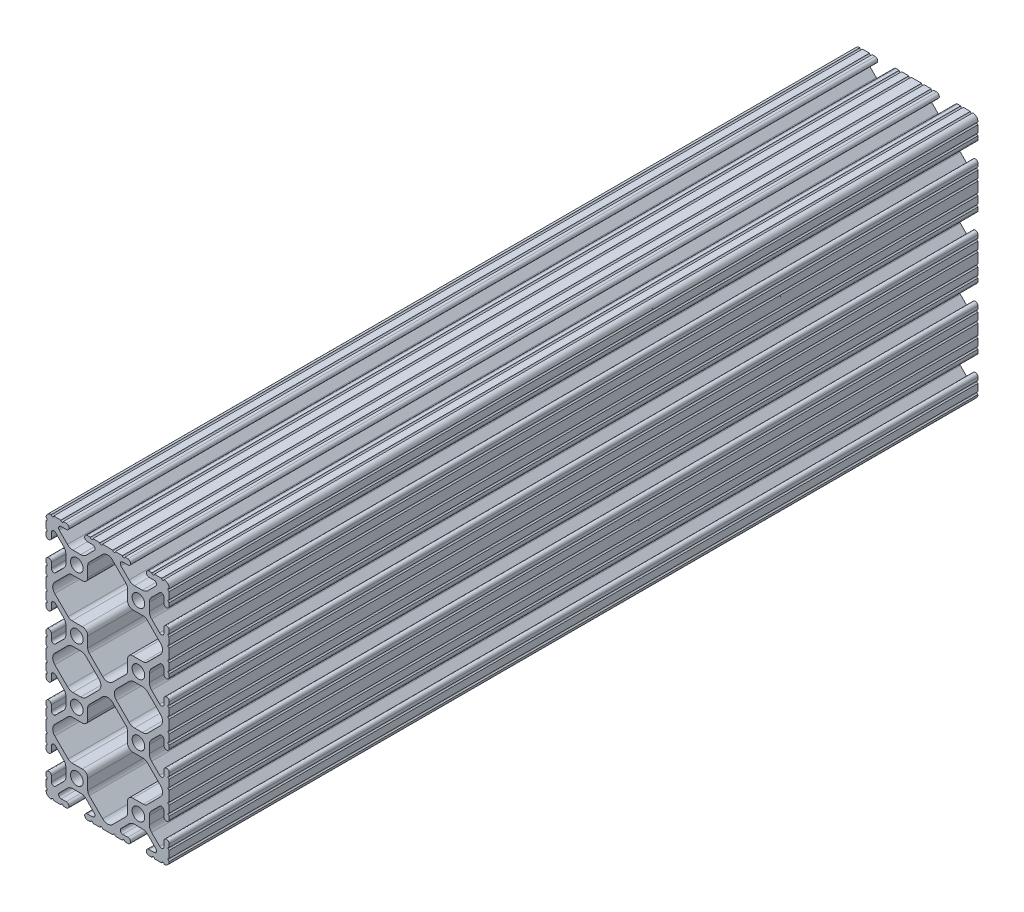
SolidWorks part; units mm, degrees
ref_plane "Front Plane" through (0, 0, 0) normal (0, 0, 1) x (1, 0, 0)
ref_plane "Top Plane" through (0, 0, 0) normal (0, 1, 0) x (1, 0, 0)
ref_plane "Right Plane" through (0, 0, 0) normal (1, 0, 0) x (0, 0, -1)
sketch "Sketch1" plane through (0, 0, 0) normal (0, 0, 1) x (1, 0, 0)
  line L0 (2.286, 55.2958) -> (-2.0184, 55.2958)
  line L1 (-3.5809, 55.943) -> (-9.0725, 61.4345)
  line L2 (-9.0725, 65.5655) -> (-3.5809, 71.057)
  line L3 (-2.0184, 71.7042) -> (2.286, 71.7042)
  line L4 (4.4958, 73.914) -> (4.4958, 78.2184)
  line L5 (5.143, 79.7809) -> (10.6345, 85.2725)
  line L6 (14.7655, 85.2725) -> (20.257, 79.7809)
  line L7 (20.9042, 78.2184) -> (20.9042, 73.914)
  line L8 (23.114, 71.7042) -> (27.4184, 71.7042)
  line L9 (28.9809, 71.057) -> (34.4725, 65.5655)
  line L10 (34.4725, 61.4345) -> (28.9809, 55.943)
  line L11 (27.4184, 55.2958) -> (23.114, 55.2958)
  line L12 (20.9042, 53.086) -> (20.9042, 48.7816)
  line L13 (20.257, 47.2191) -> (14.7655, 41.7275)
  line L14 (10.6345, 41.7275) -> (5.143, 47.2191)
  line L15 (4.4958, 48.7816) -> (4.4958, 53.086)
  line L16 (4.4958, 23.114) -> (4.4958, 27.4184)
  line L17 (5.143, 28.9809) -> (10.6345, 34.4725)
  line L18 (14.7655, 34.4725) -> (20.257, 28.9809)
  line L19 (20.9042, 27.4184) -> (20.9042, 23.114)
  line L20 (23.114, 20.9042) -> (27.4184, 20.9042)
  line L21 (28.9809, 20.257) -> (34.4725, 14.7655)
  line L22 (34.4725, 10.6345) -> (28.9809, 5.143)
  line L23 (27.4184, 4.4958) -> (23.114, 4.4958)
  line L24 (20.9042, 2.286) -> (20.9042, -2.0184)
  line L25 (20.257, -3.5809) -> (14.7655, -9.0725)
  line L26 (10.6345, -9.0725) -> (5.143, -3.5809)
  line L27 (4.4958, -2.0184) -> (4.4958, 2.286)
  line L28 (2.286, 4.4958) -> (-2.0184, 4.4958)
  line L29 (-3.5809, 5.143) -> (-9.0725, 10.6345)
  line L30 (-9.0725, 14.7655) -> (-3.5809, 20.257)
  line L31 (-2.0184, 20.9042) -> (2.286, 20.9042)
  line L32 (27.0186, 29.8958) -> (23.7824, 29.8958)
  line L33 (21.5373, 30.8258) -> (16.3286, 36.0346)
  line L34 (16.3286, 40.1654) -> (21.5373, 45.3742)
  line L35 (23.7824, 46.3042) -> (27.0186, 46.3042)
  line L36 (29.2636, 45.3743) -> (34.4725, 40.1655)
  line L37 (34.4725, 36.0345) -> (29.2636, 30.8257)
  line L38 (1.6176, 29.8958) -> (-1.6186, 29.8958)
  line L39 (-3.8636, 30.8257) -> (-9.0725, 36.0345)
  line L40 (-9.0725, 40.1655) -> (-3.8636, 45.3743)
  line L41 (-1.6186, 46.3042) -> (1.6176, 46.3042)
  line L42 (3.8627, 45.3742) -> (9.0714, 40.1654)
  line L43 (9.0714, 36.0346) -> (3.8627, 30.8258)
  line L44 (-12.7, 40.2336) -> (-12.7, 35.9664)
  line L45 (-12.7, 34.9504) -> (-12.7, 32.004)
  line L46 (-12.7, 30.988) -> (-12.7, 29.7434)
  line L47 (-10.4902, 29.7434) -> (-10.4902, 31.8743)
  line L48 (-8.7558, 32.5927) -> (-5.4258, 29.2627)
  line L49 (-4.4958, 27.0176) -> (-4.4958, 23.7824)
  line L50 (-5.4258, 21.5373) -> (-8.7558, 18.2073)
  line L51 (-10.4902, 18.9257) -> (-10.4902, 21.0566)
  line L52 (-12.7, 21.0566) -> (-12.7, 19.812)
  line L53 (-12.7, 18.796) -> (-12.7, 15.8496)
  line L54 (-12.7, 14.8336) -> (-12.7, 10.5664)
  line L55 (-12.7, 9.5504) -> (-12.7, 6.604)
  line L56 (-12.7, 5.588) -> (-12.7, 4.3434)
  line L57 (-10.4902, 4.3434) -> (-10.4902, 6.4743)
  line L58 (-8.7558, 7.1927) -> (-5.4258, 3.8627)
  line L59 (-4.4958, 1.6176) -> (-4.4958, -1.6176)
  line L60 (-5.4258, -3.8627) -> (-8.7558, -7.1927)
  line L61 (-10.4902, -6.4743) -> (-10.4902, -4.3434)
  line L62 (-12.7, -4.3434) -> (-12.7, -5.588)
  line L63 (-12.7, -6.604) -> (-12.7, -9.5504)
  line L64 (-9.5504, -12.7) -> (-6.604, -12.7)
  line L65 (-5.588, -12.7) -> (-4.3434, -12.7)
  line L66 (-4.3434, -10.4902) -> (-6.4743, -10.4902)
  line L67 (-7.1927, -8.7558) -> (-3.8627, -5.4258)
  line L68 (-1.6176, -4.4958) -> (1.6176, -4.4958)
  line L69 (3.8627, -5.4258) -> (7.1927, -8.7558)
  line L70 (6.4743, -10.4902) -> (4.3434, -10.4902)
  line L71 (4.3434, -12.7) -> (5.588, -12.7)
  line L72 (6.604, -12.7) -> (9.5504, -12.7)
  line L73 (10.5664, -12.7) -> (14.8336, -12.7)
  line L74 (15.8496, -12.7) -> (18.796, -12.7)
  line L75 (19.812, -12.7) -> (21.0566, -12.7)
  line L76 (21.0566, -10.4902) -> (18.9257, -10.4902)
  line L77 (18.2073, -8.7558) -> (21.5373, -5.4258)
  line L78 (23.7824, -4.4958) -> (27.0176, -4.4958)
  line L79 (29.2627, -5.4258) -> (32.5927, -8.7558)
  line L80 (31.8743, -10.4902) -> (29.7434, -10.4902)
  line L81 (29.7434, -12.7) -> (30.988, -12.7)
  line L82 (32.004, -12.7) -> (34.9504, -12.7)
  line L83 (38.1, -9.5504) -> (38.1, -6.604)
  line L84 (38.1, -5.588) -> (38.1, -4.3434)
  line L85 (35.8902, -4.3434) -> (35.8902, -6.4743)
  line L86 (34.1558, -7.1927) -> (30.8258, -3.8627)
  line L87 (29.8958, -1.6176) -> (29.8958, 1.6176)
  line L88 (30.8258, 3.8627) -> (34.1558, 7.1927)
  line L89 (35.8902, 6.4743) -> (35.8902, 4.3434)
  line L90 (38.1, 4.3434) -> (38.1, 5.588)
  line L91 (38.1, 6.604) -> (38.1, 9.5504)
  line L92 (38.1, 10.5664) -> (38.1, 14.8336)
  line L93 (38.1, 15.8496) -> (38.1, 18.796)
  line L94 (38.1, 19.812) -> (38.1, 21.0566)
  line L95 (35.8902, 21.0566) -> (35.8902, 18.9257)
  line L96 (34.1558, 18.2073) -> (30.8258, 21.5373)
  line L97 (29.8958, 23.7824) -> (29.8958, 27.0176)
  line L98 (30.8258, 29.2627) -> (34.1558, 32.5927)
  line L99 (35.8902, 31.8743) -> (35.8902, 29.7434)
  line L100 (38.1, 29.7434) -> (38.1, 30.988)
  line L101 (38.1, 32.004) -> (38.1, 34.9504)
  line L102 (38.1, 35.9664) -> (38.1, 40.2336)
  line L103 (38.1, 41.2496) -> (38.1, 44.196)
  line L104 (38.1, 45.212) -> (38.1, 46.4566)
  line L105 (35.8902, 46.4566) -> (35.8902, 44.3257)
  line L106 (34.1558, 43.6073) -> (30.8258, 46.9373)
  line L107 (29.8958, 49.1824) -> (29.8958, 52.4176)
  line L108 (30.8258, 54.6627) -> (34.1558, 57.9927)
  line L109 (35.8902, 57.2743) -> (35.8902, 55.1434)
  line L110 (38.1, 55.1434) -> (38.1, 56.388)
  line L111 (38.1, 57.404) -> (38.1, 60.3504)
  line L112 (38.1, 61.3664) -> (38.1, 65.6336)
  line L113 (38.1, 66.6496) -> (38.1, 69.596)
  line L114 (38.1, 70.612) -> (38.1, 71.8566)
  line L115 (35.8902, 71.8566) -> (35.8902, 69.7257)
  line L116 (34.1558, 69.0073) -> (30.8258, 72.3373)
  line L117 (29.8958, 74.5824) -> (29.8958, 77.8176)
  line L118 (30.8258, 80.0627) -> (34.1558, 83.3927)
  line L119 (35.8902, 82.6743) -> (35.8902, 80.5434)
  line L120 (38.1, 80.5434) -> (38.1, 81.788)
  line L121 (38.1, 82.804) -> (38.1, 85.7504)
  line L122 (34.9504, 88.9) -> (32.004, 88.9)
  line L123 (30.988, 88.9) -> (29.7434, 88.9)
  line L124 (29.7434, 86.6902) -> (31.8743, 86.6902)
  line L125 (32.5927, 84.9558) -> (29.2627, 81.6258)
  line L126 (27.0176, 80.6958) -> (23.7824, 80.6958)
  line L127 (21.5373, 81.6258) -> (18.2073, 84.9558)
  line L128 (18.9257, 86.6902) -> (21.0566, 86.6902)
  line L129 (21.0566, 88.9) -> (19.812, 88.9)
  line L130 (18.796, 88.9) -> (15.8496, 88.9)
  line L131 (14.8336, 88.9) -> (10.5664, 88.9)
  line L132 (9.5504, 88.9) -> (6.604, 88.9)
  line L133 (5.588, 88.9) -> (4.3434, 88.9)
  line L134 (4.3434, 86.6902) -> (6.4743, 86.6902)
  line L135 (7.1927, 84.9558) -> (3.8627, 81.6258)
  line L136 (1.6176, 80.6958) -> (-1.6176, 80.6958)
  line L137 (-3.8627, 81.6258) -> (-7.1927, 84.9558)
  line L138 (-6.4743, 86.6902) -> (-4.3434, 86.6902)
  line L139 (-4.3434, 88.9) -> (-5.588, 88.9)
  line L140 (-6.604, 88.9) -> (-9.5504, 88.9)
  line L141 (-12.7, 85.7504) -> (-12.7, 82.804)
  line L142 (-12.7, 81.788) -> (-12.7, 80.5434)
  line L143 (-10.4902, 80.5434) -> (-10.4902, 82.6743)
  line L144 (-8.7558, 83.3927) -> (-5.4258, 80.0627)
  line L145 (-4.4958, 77.8176) -> (-4.4958, 74.5824)
  line L146 (-5.4258, 72.3373) -> (-8.7558, 69.0073)
  line L147 (-10.4902, 69.7257) -> (-10.4902, 71.8566)
  line L148 (-12.7, 71.8566) -> (-12.7, 70.612)
  line L149 (-12.7, 69.596) -> (-12.7, 66.6496)
  line L150 (-12.7, 65.6336) -> (-12.7, 61.3664)
  line L151 (-12.7, 60.3504) -> (-12.7, 57.404)
  line L152 (-12.7, 56.388) -> (-12.7, 55.1434)
  line L153 (-10.4902, 55.1434) -> (-10.4902, 57.2743)
  line L154 (-8.7558, 57.9927) -> (-5.4258, 54.6627)
  line L155 (-4.4958, 52.4176) -> (-4.4958, 49.1824)
  line L156 (-5.4258, 46.9373) -> (-8.7558, 43.6073)
  line L157 (-10.4902, 44.3257) -> (-10.4902, 46.4566)
  line L158 (-12.7, 46.4566) -> (-12.7, 45.212)
  line L159 (-12.7, 44.196) -> (-12.7, 41.2496)
  arc A0 (4.4958, 53.086) -> (2.286, 55.2958) centre (2.286, 53.086) ccw
  arc A1 (-3.5809, 55.943) -> (-2.0184, 55.2958) centre (-2.0184, 57.5056) ccw
  arc A2 (-9.0725, 65.5655) -> (-9.0725, 61.4345) centre (-7.0071, 63.5) ccw
  arc A3 (-2.0184, 71.7042) -> (-3.5809, 71.057) centre (-2.0184, 69.4944) ccw
  arc A4 (2.286, 71.7042) -> (4.4958, 73.914) centre (2.286, 73.914) ccw
  arc A5 (5.143, 79.7809) -> (4.4958, 78.2184) centre (6.7056, 78.2184) ccw
  arc A6 (14.7655, 85.2725) -> (10.6345, 85.2725) centre (12.7, 83.2071) ccw
  arc A7 (20.9042, 78.2184) -> (20.257, 79.7809) centre (18.6944, 78.2184) ccw
  arc A8 (20.9042, 73.914) -> (23.114, 71.7042) centre (23.114, 73.914) ccw
  arc A9 (28.9809, 71.057) -> (27.4184, 71.7042) centre (27.4184, 69.4944) ccw
  arc A10 (34.4725, 61.4345) -> (34.4725, 65.5655) centre (32.4071, 63.5) ccw
  arc A11 (27.4184, 55.2958) -> (28.9809, 55.943) centre (27.4184, 57.5056) ccw
  arc A12 (23.114, 55.2958) -> (20.9042, 53.086) centre (23.114, 53.086) ccw
  arc A13 (20.257, 47.2191) -> (20.9042, 48.7816) centre (18.6944, 48.7816) ccw
  arc A14 (10.6345, 41.7275) -> (14.7655, 41.7275) centre (12.7, 43.7929) ccw
  arc A15 (4.4958, 48.7816) -> (5.143, 47.2191) centre (6.7056, 48.7816) ccw
  arc A16 (2.286, 20.9042) -> (4.4958, 23.114) centre (2.286, 23.114) ccw
  arc A17 (5.143, 28.9809) -> (4.4958, 27.4184) centre (6.7056, 27.4184) ccw
  arc A18 (14.7655, 34.4725) -> (10.6345, 34.4725) centre (12.7, 32.4071) ccw
  arc A19 (20.9042, 27.4184) -> (20.257, 28.9809) centre (18.6944, 27.4184) ccw
  arc A20 (20.9042, 23.114) -> (23.114, 20.9042) centre (23.114, 23.114) ccw
  arc A21 (28.9809, 20.257) -> (27.4184, 20.9042) centre (27.4184, 18.6944) ccw
  arc A22 (34.4725, 10.6345) -> (34.4725, 14.7655) centre (32.4071, 12.7) ccw
  arc A23 (27.4184, 4.4958) -> (28.9809, 5.143) centre (27.4184, 6.7056) ccw
  arc A24 (23.114, 4.4958) -> (20.9042, 2.286) centre (23.114, 2.286) ccw
  arc A25 (20.257, -3.5809) -> (20.9042, -2.0184) centre (18.6944, -2.0184) ccw
  arc A26 (10.6345, -9.0725) -> (14.7655, -9.0725) centre (12.7, -7.0071) ccw
  arc A27 (4.4958, -2.0184) -> (5.143, -3.5809) centre (6.7056, -2.0184) ccw
  arc A28 (4.4958, 2.286) -> (2.286, 4.4958) centre (2.286, 2.286) ccw
  arc A29 (-3.5809, 5.143) -> (-2.0184, 4.4958) centre (-2.0184, 6.7056) ccw
  arc A30 (-9.0725, 14.7655) -> (-9.0725, 10.6345) centre (-7.0071, 12.7) ccw
  arc A31 (-2.0184, 20.9042) -> (-3.5809, 20.257) centre (-2.0184, 18.6944) ccw
  arc A32 (27.0186, 29.8958) -> (29.2636, 30.8257) centre (27.0186, 33.0708) ccw
  arc A33 (21.5373, 30.8258) -> (23.7824, 29.8958) centre (23.7824, 33.0708) ccw
  arc A34 (16.3286, 40.1654) -> (16.3286, 36.0346) centre (18.3941, 38.1) ccw
  arc A35 (23.7824, 46.3042) -> (21.5373, 45.3742) centre (23.7824, 43.1292) ccw
  arc A36 (29.2636, 45.3743) -> (27.0186, 46.3042) centre (27.0186, 43.1292) ccw
  arc A37 (34.4725, 36.0345) -> (34.4725, 40.1655) centre (32.4071, 38.1) ccw
  arc A38 (1.6176, 29.8958) -> (3.8627, 30.8258) centre (1.6176, 33.0708) ccw
  arc A39 (-3.8636, 30.8257) -> (-1.6186, 29.8958) centre (-1.6186, 33.0708) ccw
  arc A40 (-9.0725, 40.1655) -> (-9.0725, 36.0345) centre (-7.0071, 38.1) ccw
  arc A41 (-1.6186, 46.3042) -> (-3.8636, 45.3743) centre (-1.6186, 43.1292) ccw
  arc A42 (3.8627, 45.3742) -> (1.6176, 46.3042) centre (1.6176, 43.1292) ccw
  arc A43 (9.0714, 36.0346) -> (9.0714, 40.1654) centre (7.0059, 38.1) ccw
  circle A44 centre (25.4, 76.2) radius 2.6035
  circle A45 centre (0, 76.2) radius 2.6035
  circle A46 centre (25.4, 50.8) radius 2.6035
  circle A47 centre (0, 50.8) radius 2.6035
  circle A48 centre (25.4, 0) radius 2.6035
  circle A49 centre (0, 0) radius 2.6035
  circle A50 centre (25.4, 25.4) radius 2.6035
  circle A51 centre (0, 25.4) radius 2.6035
  arc A52 (-12.7, 34.9504) -> (-12.7, 35.9664) centre (-12.7, 35.4584) ccw
  arc A53 (-12.7, 30.988) -> (-12.7, 32.004) centre (-12.7, 31.496) ccw
  arc A54 (-12.7, 29.7434) -> (-10.4902, 29.7434) centre (-11.5951, 29.7434) ccw
  arc A55 (-8.7558, 32.5927) -> (-10.4902, 31.8743) centre (-9.4742, 31.8743) ccw
  arc A56 (-4.4958, 27.0176) -> (-5.4258, 29.2627) centre (-7.6708, 27.0176) ccw
  arc A57 (-5.4258, 21.5373) -> (-4.4958, 23.7824) centre (-7.6708, 23.7824) ccw
  arc A58 (-10.4902, 18.9257) -> (-8.7558, 18.2073) centre (-9.4742, 18.9257) ccw
  arc A59 (-10.4902, 21.0566) -> (-12.7, 21.0566) centre (-11.5951, 21.0566) ccw
  arc A60 (-12.7, 18.796) -> (-12.7, 19.812) centre (-12.7, 19.304) ccw
  arc A61 (-12.7, 14.8336) -> (-12.7, 15.8496) centre (-12.7, 15.3416) ccw
  arc A62 (-12.7, 9.5504) -> (-12.7, 10.5664) centre (-12.7, 10.0584) ccw
  arc A63 (-12.7, 5.588) -> (-12.7, 6.604) centre (-12.7, 6.096) ccw
  arc A64 (-12.7, 4.3434) -> (-10.4902, 4.3434) centre (-11.5951, 4.3434) ccw
  arc A65 (-8.7558, 7.1927) -> (-10.4902, 6.4743) centre (-9.4742, 6.4743) ccw
  arc A66 (-4.4958, 1.6176) -> (-5.4258, 3.8627) centre (-7.6708, 1.6176) ccw
  arc A67 (-5.4258, -3.8627) -> (-4.4958, -1.6176) centre (-7.6708, -1.6176) ccw
  arc A68 (-10.4902, -6.4743) -> (-8.7558, -7.1927) centre (-9.4742, -6.4743) ccw
  arc A69 (-10.4902, -4.3434) -> (-12.7, -4.3434) centre (-11.5951, -4.3434) ccw
  arc A70 (-12.7, -6.604) -> (-12.7, -5.588) centre (-12.7, -6.096) ccw
  arc A71 (-12.6998, -10.5664) -> (-12.7, -9.5504) centre (-12.7, -10.0584) ccw
  arc A72 (-12.6998, -10.5664) -> (-10.5664, -12.6998) centre (-10.5918, -10.5918) ccw
  arc A73 (-9.5504, -12.7) -> (-10.5664, -12.6998) centre (-10.0584, -12.7) ccw
  arc A74 (-5.588, -12.7) -> (-6.604, -12.7) centre (-6.096, -12.7) ccw
  arc A75 (-4.3434, -12.7) -> (-4.3434, -10.4902) centre (-4.3434, -11.5951) ccw
  arc A76 (-7.1927, -8.7558) -> (-6.4743, -10.4902) centre (-6.4743, -9.4742) ccw
  arc A77 (-1.6176, -4.4958) -> (-3.8627, -5.4258) centre (-1.6176, -7.6708) ccw
  arc A78 (3.8627, -5.4258) -> (1.6176, -4.4958) centre (1.6176, -7.6708) ccw
  arc A79 (6.4743, -10.4902) -> (7.1927, -8.7558) centre (6.4743, -9.4742) ccw
  arc A80 (4.3434, -10.4902) -> (4.3434, -12.7) centre (4.3434, -11.5951) ccw
  arc A81 (6.604, -12.7) -> (5.588, -12.7) centre (6.096, -12.7) ccw
  arc A82 (10.5664, -12.7) -> (9.5504, -12.7) centre (10.0584, -12.7) ccw
  arc A83 (15.8496, -12.7) -> (14.8336, -12.7) centre (15.3416, -12.7) ccw
  arc A84 (19.812, -12.7) -> (18.796, -12.7) centre (19.304, -12.7) ccw
  arc A85 (21.0566, -12.7) -> (21.0566, -10.4902) centre (21.0566, -11.5951) ccw
  arc A86 (18.2073, -8.7558) -> (18.9257, -10.4902) centre (18.9257, -9.4742) ccw
  arc A87 (23.7824, -4.4958) -> (21.5373, -5.4258) centre (23.7824, -7.6708) ccw
  arc A88 (29.2627, -5.4258) -> (27.0176, -4.4958) centre (27.0176, -7.6708) ccw
  arc A89 (31.8743, -10.4902) -> (32.5927, -8.7558) centre (31.8743, -9.4742) ccw
  arc A90 (29.7434, -10.4902) -> (29.7434, -12.7) centre (29.7434, -11.5951) ccw
  arc A91 (32.004, -12.7) -> (30.988, -12.7) centre (31.496, -12.7) ccw
  arc A92 (35.9664, -12.6998) -> (34.9504, -12.7) centre (35.4584, -12.7) ccw
  arc A93 (35.9664, -12.6998) -> (38.0998, -10.5664) centre (35.9918, -10.5918) ccw
  arc A94 (38.1, -9.5504) -> (38.0998, -10.5664) centre (38.1, -10.0584) ccw
  arc A95 (38.1, -5.588) -> (38.1, -6.604) centre (38.1, -6.096) ccw
  arc A96 (38.1, -4.3434) -> (35.8902, -4.3434) centre (36.9951, -4.3434) ccw
  arc A97 (34.1558, -7.1927) -> (35.8902, -6.4743) centre (34.8742, -6.4743) ccw
  arc A98 (29.8958, -1.6176) -> (30.8258, -3.8627) centre (33.0708, -1.6176) ccw
  arc A99 (30.8258, 3.8627) -> (29.8958, 1.6176) centre (33.0708, 1.6176) ccw
  arc A100 (35.8902, 6.4743) -> (34.1558, 7.1927) centre (34.8742, 6.4743) ccw
  arc A101 (35.8902, 4.3434) -> (38.1, 4.3434) centre (36.9951, 4.3434) ccw
  arc A102 (38.1, 6.604) -> (38.1, 5.588) centre (38.1, 6.096) ccw
  arc A103 (38.1, 10.5664) -> (38.1, 9.5504) centre (38.1, 10.0584) ccw
  arc A104 (38.1, 15.8496) -> (38.1, 14.8336) centre (38.1, 15.3416) ccw
  arc A105 (38.1, 19.812) -> (38.1, 18.796) centre (38.1, 19.304) ccw
  arc A106 (38.1, 21.0566) -> (35.8902, 21.0566) centre (36.9951, 21.0566) ccw
  arc A107 (34.1558, 18.2073) -> (35.8902, 18.9257) centre (34.8742, 18.9257) ccw
  arc A108 (29.8958, 23.7824) -> (30.8258, 21.5373) centre (33.0708, 23.7824) ccw
  arc A109 (30.8258, 29.2627) -> (29.8958, 27.0176) centre (33.0708, 27.0176) ccw
  arc A110 (35.8902, 31.8743) -> (34.1558, 32.5927) centre (34.8742, 31.8743) ccw
  arc A111 (35.8902, 29.7434) -> (38.1, 29.7434) centre (36.9951, 29.7434) ccw
  arc A112 (38.1, 32.004) -> (38.1, 30.988) centre (38.1, 31.496) ccw
  arc A113 (38.1, 35.9664) -> (38.1, 34.9504) centre (38.1, 35.4584) ccw
  arc A114 (38.1, 41.2496) -> (38.1, 40.2336) centre (38.1, 40.7416) ccw
  arc A115 (38.1, 45.212) -> (38.1, 44.196) centre (38.1, 44.704) ccw
  arc A116 (38.1, 46.4566) -> (35.8902, 46.4566) centre (36.9951, 46.4566) ccw
  arc A117 (34.1558, 43.6073) -> (35.8902, 44.3257) centre (34.8742, 44.3257) ccw
  arc A118 (29.8958, 49.1824) -> (30.8258, 46.9373) centre (33.0708, 49.1824) ccw
  arc A119 (30.8258, 54.6627) -> (29.8958, 52.4176) centre (33.0708, 52.4176) ccw
  arc A120 (35.8902, 57.2743) -> (34.1558, 57.9927) centre (34.8742, 57.2743) ccw
  arc A121 (35.8902, 55.1434) -> (38.1, 55.1434) centre (36.9951, 55.1434) ccw
  arc A122 (38.1, 57.404) -> (38.1, 56.388) centre (38.1, 56.896) ccw
  arc A123 (38.1, 61.3664) -> (38.1, 60.3504) centre (38.1, 60.8584) ccw
  arc A124 (38.1, 66.6496) -> (38.1, 65.6336) centre (38.1, 66.1416) ccw
  arc A125 (38.1, 70.612) -> (38.1, 69.596) centre (38.1, 70.104) ccw
  arc A126 (38.1, 71.8566) -> (35.8902, 71.8566) centre (36.9951, 71.8566) ccw
  arc A127 (34.1558, 69.0073) -> (35.8902, 69.7257) centre (34.8742, 69.7257) ccw
  arc A128 (29.8958, 74.5824) -> (30.8258, 72.3373) centre (33.0708, 74.5824) ccw
  arc A129 (30.8258, 80.0627) -> (29.8958, 77.8176) centre (33.0708, 77.8176) ccw
  arc A130 (35.8902, 82.6743) -> (34.1558, 83.3927) centre (34.8742, 82.6743) ccw
  arc A131 (35.8902, 80.5434) -> (38.1, 80.5434) centre (36.9951, 80.5434) ccw
  arc A132 (38.1, 82.804) -> (38.1, 81.788) centre (38.1, 82.296) ccw
  arc A133 (38.0998, 86.7664) -> (38.1, 85.7504) centre (38.1, 86.2584) ccw
  arc A134 (38.0998, 86.7664) -> (35.9664, 88.8998) centre (35.9918, 86.7918) ccw
  arc A135 (34.9504, 88.9) -> (35.9664, 88.8998) centre (35.4584, 88.9) ccw
  arc A136 (30.988, 88.9) -> (32.004, 88.9) centre (31.496, 88.9) ccw
  arc A137 (29.7434, 88.9) -> (29.7434, 86.6902) centre (29.7434, 87.7951) ccw
  arc A138 (32.5927, 84.9558) -> (31.8743, 86.6902) centre (31.8743, 85.6742) ccw
  arc A139 (27.0176, 80.6958) -> (29.2627, 81.6258) centre (27.0176, 83.8708) ccw
  arc A140 (21.5373, 81.6258) -> (23.7824, 80.6958) centre (23.7824, 83.8708) ccw
  arc A141 (18.9257, 86.6902) -> (18.2073, 84.9558) centre (18.9257, 85.6742) ccw
  arc A142 (21.0566, 86.6902) -> (21.0566, 88.9) centre (21.0566, 87.7951) ccw
  arc A143 (18.796, 88.9) -> (19.812, 88.9) centre (19.304, 88.9) ccw
  arc A144 (14.8336, 88.9) -> (15.8496, 88.9) centre (15.3416, 88.9) ccw
  arc A145 (9.5504, 88.9) -> (10.5664, 88.9) centre (10.0584, 88.9) ccw
  arc A146 (5.588, 88.9) -> (6.604, 88.9) centre (6.096, 88.9) ccw
  arc A147 (4.3434, 88.9) -> (4.3434, 86.6902) centre (4.3434, 87.7951) ccw
  arc A148 (7.1927, 84.9558) -> (6.4743, 86.6902) centre (6.4743, 85.6742) ccw
  arc A149 (1.6176, 80.6958) -> (3.8627, 81.6258) centre (1.6176, 83.8708) ccw
  arc A150 (-3.8627, 81.6258) -> (-1.6176, 80.6958) centre (-1.6176, 83.8708) ccw
  arc A151 (-6.4743, 86.6902) -> (-7.1927, 84.9558) centre (-6.4743, 85.6742) ccw
  arc A152 (-4.3434, 86.6902) -> (-4.3434, 88.9) centre (-4.3434, 87.7951) ccw
  arc A153 (-6.604, 88.9) -> (-5.588, 88.9) centre (-6.096, 88.9) ccw
  arc A154 (-10.5664, 88.8998) -> (-9.5504, 88.9) centre (-10.0584, 88.9) ccw
  arc A155 (-10.5664, 88.8998) -> (-12.6998, 86.7664) centre (-10.5918, 86.7918) ccw
  arc A156 (-12.7, 85.7504) -> (-12.6998, 86.7664) centre (-12.7, 86.2584) ccw
  arc A157 (-12.7, 81.788) -> (-12.7, 82.804) centre (-12.7, 82.296) ccw
  arc A158 (-12.7, 80.5434) -> (-10.4902, 80.5434) centre (-11.5951, 80.5434) ccw
  arc A159 (-8.7558, 83.3927) -> (-10.4902, 82.6743) centre (-9.4742, 82.6743) ccw
  arc A160 (-4.4958, 77.8176) -> (-5.4258, 80.0627) centre (-7.6708, 77.8176) ccw
  arc A161 (-5.4258, 72.3373) -> (-4.4958, 74.5824) centre (-7.6708, 74.5824) ccw
  arc A162 (-10.4902, 69.7257) -> (-8.7558, 69.0073) centre (-9.4742, 69.7257) ccw
  arc A163 (-10.4902, 71.8566) -> (-12.7, 71.8566) centre (-11.5951, 71.8566) ccw
  arc A164 (-12.7, 69.596) -> (-12.7, 70.612) centre (-12.7, 70.104) ccw
  arc A165 (-12.7, 65.6336) -> (-12.7, 66.6496) centre (-12.7, 66.1416) ccw
  arc A166 (-12.7, 60.3504) -> (-12.7, 61.3664) centre (-12.7, 60.8584) ccw
  arc A167 (-12.7, 56.388) -> (-12.7, 57.404) centre (-12.7, 56.896) ccw
  arc A168 (-12.7, 55.1434) -> (-10.4902, 55.1434) centre (-11.5951, 55.1434) ccw
  arc A169 (-8.7558, 57.9927) -> (-10.4902, 57.2743) centre (-9.4742, 57.2743) ccw
  arc A170 (-4.4958, 52.4176) -> (-5.4258, 54.6627) centre (-7.6708, 52.4176) ccw
  arc A171 (-5.4258, 46.9373) -> (-4.4958, 49.1824) centre (-7.6708, 49.1824) ccw
  arc A172 (-10.4902, 44.3257) -> (-8.7558, 43.6073) centre (-9.4742, 44.3257) ccw
  arc A173 (-10.4902, 46.4566) -> (-12.7, 46.4566) centre (-11.5951, 46.4566) ccw
  arc A174 (-12.7, 44.196) -> (-12.7, 45.212) centre (-12.7, 44.704) ccw
  arc A175 (-12.7, 40.2336) -> (-12.7, 41.2496) centre (-12.7, 40.7416) ccw
extrude "Extrude1" add sketch "Sketch1" against normal blind 333.375
